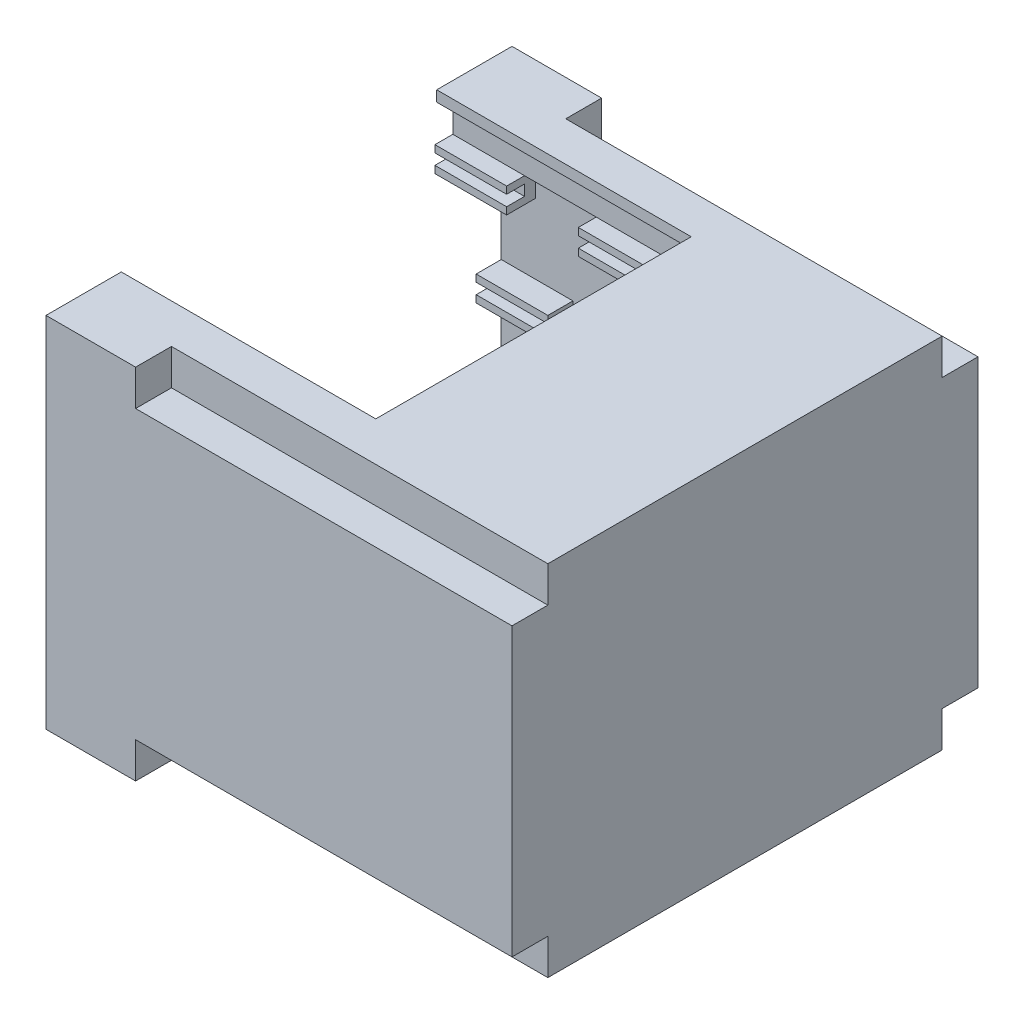
SolidWorks part; units mm, degrees
ref_plane "Front Plane" through (0, 0, 0) normal (0, 0, 1) x (1, 0, 0)
ref_plane "Top Plane" through (0, 0, 0) normal (0, 1, 0) x (1, 0, 0)
ref_plane "Right Plane" through (0, 0, 0) normal (1, 0, 0) x (0, 0, -1)
sketch "Sketch2" plane through (0, 0, 0) normal (0, 1, 0) x (1, 0, 0)
  line L1 (0, 0) -> (130, 0)
  line L2 (0, 0) -> (0, 130)
  line L3 (0, 130) -> (130, 130)
  line L4 (130, 0) -> (130, 130)
  dimension "D1" = 130
  dimension "D2" = 130
extrude "Boss-Extrude1" add sketch "Sketch2" along normal blind 100
sketch "Sketch3" plane through (0, 0, 0) normal (-1, 0, 0) x (0, 0, 1)
  line L0 (-130, 100) -> (0, 100) construction
  line L1 (-117, 13) -> (-13, 13)
  line L2 (-117, 13) -> (-117, 87)
  line L3 (-117, 87) -> (-13, 87)
  line L4 (-13, 13) -> (-13, 87)
  line L5 (0, 100) -> (0, 0) construction
  line L6 (-130, 0) -> (0, 0) construction
  line L7 (-130, 100) -> (-130, 0) construction
  dimension "D1" = 13
  dimension "D2" = 13
  dimension "D3" = 13
  dimension "D4" = 13
extrude "Cut-Extrude1" cut sketch "Sketch3" against normal blind 127
sketch "Sketch4" plane through (130, 0, 0) normal (1, 0, 0) x (0, 0, -1)
  line L1 (0, 100) -> (10, 100)
  line L2 (0, 100) -> (0, 90)
  line L3 (0, 90) -> (10, 90)
  line L4 (10, 100) -> (10, 90)
  line L5 (130, 100) -> (120, 100)
  line L6 (130, 100) -> (130, 90)
  line L7 (130, 90) -> (120, 90)
  line L8 (120, 100) -> (120, 90)
  line L9 (0, 0) -> (10, 0)
  line L10 (0, 0) -> (0, 10)
  line L11 (0, 10) -> (10, 10)
  line L12 (10, 0) -> (10, 10)
  line L13 (130, 0) -> (120, 0)
  line L14 (130, 0) -> (130, 10)
  line L15 (130, 10) -> (120, 10)
  line L16 (120, 0) -> (120, 10)
  dimension "D1" = 10
  dimension "D2" = 10
  dimension "D3" = 10
  dimension "D4" = 10
  dimension "D5" = 10
  dimension "D6" = 10
  dimension "D7" = 10
  dimension "D8" = 10
extrude "Cut-Extrude3" cut sketch "Sketch4" against normal blind 105
sketch "Sketch5" plane through (0, 0, 0) normal (-1, 0, 0) x (0, 0, 1)
  line L0 (-130, 100) -> (0, 100) construction
  line L1 (-117, 87) -> (-13, 87)
  line L2 (-117, 87) -> (-117, 97)
  line L3 (-117, 97) -> (-13, 97)
  line L4 (-13, 87) -> (-13, 97)
  line L5 (-117, 13) -> (-13, 13)
  line L6 (-117, 13) -> (-117, 3)
  line L7 (-117, 3) -> (-13, 3)
  line L8 (-13, 13) -> (-13, 3)
  line L9 (-130, 0) -> (0, 0) construction
  line L10 (0, 100) -> (0, 0) construction
  dimension "D1" = 3
  dimension "D2" = 3
  dimension "D3" = 13
  dimension "D4" = 13
extrude "Cut-Extrude4" cut sketch "Sketch5" against normal blind 127
sketch "Sketch6" plane through (0, 0, 0) normal (-1, 0, 0) x (0, 0, 1)
  line L0 (-117, 97) -> (-117, 3) construction
  line L1 (-117, 87) -> (-127, 87)
  line L2 (-117, 87) -> (-117, 13)
  line L3 (-117, 13) -> (-127, 13)
  line L4 (-127, 87) -> (-127, 13)
  line L5 (-13, 3) -> (-13, 97) construction
  line L6 (-13, 87) -> (-3, 87)
  line L7 (-13, 87) -> (-13, 13)
  line L8 (-13, 13) -> (-3, 13)
  line L9 (-3, 87) -> (-3, 13)
  line L10 (-130, 100) -> (-130, 0) construction
  line L11 (0, 100) -> (0, 0) construction
  line L12 (-130, 100) -> (0, 100) construction
  line L13 (-130, 0) -> (0, 0) construction
  dimension "D1" = 3
  dimension "D2" = 3
  dimension "D3" = 13
  dimension "D4" = 13
  dimension "D5" = 13
  dimension "D6" = 13
extrude "Cut-Extrude5" cut sketch "Sketch6" against normal blind 127
sketch "Sketch7" plane through (0, 0, 0) normal (-1, 0, 0) x (0, 0, 1)
  line L0 (0, 100) -> (0, 0) construction
  line L1 (-130, 0) -> (0, 0) construction
  line L2 (-130, 100) -> (-130, 0) construction
  line L3 (-130, 100) -> (0, 100) construction
  circle A0 centre (-124, 94) radius 1.75
  circle A1 centre (-6, 94) radius 1.75
  circle A2 centre (-124, 6) radius 1.75
  circle A3 centre (-6, 6) radius 1.75
  dimension "D3" = 3.5
  dimension "D6" = 3.5
  dimension "D9" = 3.5
  dimension "D12" = 3.5
  dimension "D1" = 6
  dimension "D2" = 6
  dimension "D4" = 6
  dimension "D5" = 6
  dimension "D7" = 6
  dimension "D8" = 6
  dimension "D10" = 6
  dimension "D11" = 6
extrude "Cut-Extrude6" cut sketch "Sketch7" against normal blind 20
sketch "Sketch8" plane through (0, 0, 0) normal (-1, 0, 0) x (0, 0, 1)
  line L1 (-117, 87) -> (-120, 87)
  line L2 (-117, 87) -> (-117, 90)
  line L3 (-117, 90) -> (-120, 90)
  line L4 (-120, 87) -> (-120, 90)
  line L5 (-13, 87) -> (-10, 87)
  line L6 (-13, 87) -> (-13, 90)
  line L7 (-13, 90) -> (-10, 90)
  line L8 (-10, 87) -> (-10, 90)
  line L9 (-117, 13) -> (-120, 13)
  line L10 (-117, 13) -> (-117, 10)
  line L11 (-117, 10) -> (-120, 10)
  line L12 (-120, 13) -> (-120, 10)
  line L13 (-13, 13) -> (-10, 13)
  line L14 (-13, 13) -> (-13, 10)
  line L15 (-13, 10) -> (-10, 10)
  line L16 (-10, 13) -> (-10, 10)
  dimension "D1" = 3
  dimension "D2" = 3
  dimension "D3" = 3
  dimension "D4" = 3
  dimension "D5" = 3
  dimension "D6" = 3
  dimension "D7" = 3
  dimension "D8" = 3
extrude "Cut-Extrude7" cut sketch "Sketch8" against normal blind 5
sketch "Sketch9" plane through (0, 3, 0) normal (0, 1, 0) x (1, 0, 0)
  line L1 (0, 117) -> (85, 117)
  line L2 (0, 117) -> (0, 57)
  line L3 (0, 57) -> (85, 57)
  line L4 (85, 117) -> (85, 57)
  dimension "D1" = 60
  dimension "D2" = 85
extrude "Boss-Extrude2" add sketch "Sketch9" along normal blind 15
sketch "Sketch11" plane through (0, 13, 0) normal (0, 1, 0) x (1, 0, 0)
  line L0 (0, 127) -> (0, 120) construction
  line L5 (85, 117) -> (0, 117)
  line L6 (85, 117) -> (85, 123)
  line L7 (85, 123) -> (0, 123)
  line L8 (0, 117) -> (0, 123)
  dimension "D1" = 6
extrude "Boss-Extrude5" add sketch "Sketch11" along normal blind 5
sketch "Sketch12" plane through (0, 18, 0) normal (0, 1, 0) x (1, 0, 0)
  line L0 (85, 57) -> (85, 123) construction
  line L1 (0, 123) -> (85, 123)
  line L2 (0, 123) -> (0, 120)
  line L3 (0, 120) -> (85, 120)
  line L4 (85, 123) -> (85, 120)
  dimension "D1" = 3
extrude "Cut-Extrude9" cut sketch "Sketch12" against normal blind 4
sketch "Sketch13" plane through (0, 18, 0) normal (0, 1, 0) x (1, 0, 0)
  line L0 (85, 57) -> (85, 120) construction
  line L1 (82, 117) -> (0, 117)
  line L2 (82, 117) -> (82, 60)
  line L3 (82, 60) -> (0, 60)
  line L4 (0, 117) -> (0, 60)
  line L5 (0, 57) -> (85, 57) construction
  line L6 (0, 120) -> (85, 120) construction
  line L7 (0, 120) -> (0, 57) construction
  dimension "D1" = 3
  dimension "D2" = 3
  dimension "D3" = 3
  dimension "D4" = 0
extrude "Cut-Extrude10" cut sketch "Sketch13" against normal blind 15
sketch "Sketch15" plane through (5, 0, 0) normal (-1, 0, 0) x (0, 0, 1)
  line L1 (-120, 13) -> (-117, 13)
  line L2 (-120, 13) -> (-120, 10)
  line L3 (-120, 10) -> (-117, 10)
  line L4 (-117, 13) -> (-117, 10)
extrude "Boss-Extrude7" add sketch "Sketch15" along normal blind 5
sketch "Sketch16" plane through (0, 0, -60) normal (0, 0, -1) x (-1, 0, 0)
  line L0 (0, 3) -> (0, 18) construction
  line L1 (-82, 18) -> (0, 18)
  line L2 (-82, 18) -> (-82, 16)
  line L3 (-82, 16) -> (0, 16)
  line L4 (0, 18) -> (0, 16)
  line L5 (-82, 3) -> (-82, 18) construction
  line L6 (-82, 13) -> (0, 13)
  line L7 (-82, 13) -> (-82, 11)
  line L8 (-82, 11) -> (0, 11)
  line L9 (0, 13) -> (0, 11)
  dimension "D1" = 2
  dimension "D2" = 2
  dimension "D3" = 3
extrude "Boss-Extrude8" add sketch "Sketch16" along normal blind 57
sketch "Sketch17" plane through (0, 18, 0) normal (0, 1, 0) x (1, 0, 0)
  line L0 (0, 120) -> (0, 57) construction
  line L1 (0, 112) -> (77, 112)
  line L2 (0, 112) -> (0, 65)
  line L3 (0, 65) -> (77, 65)
  line L4 (77, 112) -> (77, 65)
  line L5 (0, 57) -> (85, 57) construction
  line L6 (85, 57) -> (85, 120) construction
  line L7 (0, 120) -> (85, 120) construction
  dimension "D1" = 8
  dimension "D2" = 8
  dimension "D3" = 8
extrude "Cut-Extrude11" cut sketch "Sketch17" against normal blind 10
sketch "Sketch19" plane through (0, 0, -117) normal (0, 0, 1) x (1, 0, 0)
  line L1 (0, 11) -> (7, 11)
  line L2 (0, 11) -> (0, 9)
  line L3 (0, 9) -> (7, 9)
  line L4 (7, 11) -> (7, 9)
  line L5 (0, 13) -> (7, 13)
  line L6 (0, 13) -> (0, 14)
  line L7 (0, 14) -> (7, 14)
  line L8 (7, 13) -> (7, 14)
  dimension "D1" = 2
  dimension "D2" = 7
  dimension "D3" = 7
  dimension "D4" = 1
extrude "Boss-Extrude9" add sketch "Sketch19" along normal blind 1
sketch "Sketch21" plane through (0, 0, 0) normal (-1, 0, 0) x (0, 0, 1)
  line L0 (-130, 0) -> (0, 0) construction
  line L1 (-120, 13) -> (-117, 13)
  line L2 (-120, 13) -> (-120, 10)
  line L3 (-120, 10) -> (-117, 10)
  line L4 (-117, 13) -> (-117, 10)
  line L5 (-130, 100) -> (-130, 0) construction
  dimension "D1" = 3
  dimension "D2" = 3
  dimension "D3" = 10
  dimension "D4" = 10
extrude "Cut-Extrude15" cut sketch "Sketch21" against normal blind 5
sketch "Sketch22" plane through (127, 0, 0) normal (-1, 0, 0) x (0, 0, 1)
  line L0 (-127, 87) -> (-127, 13) construction
  line L1 (-127, 50) -> (-3, 50)
  line L2 (-127, 50) -> (-127, 43)
  line L3 (-127, 43) -> (-3, 43)
  line L4 (-3, 50) -> (-3, 43)
  line L5 (-3, 13) -> (-3, 87) construction
  line L6 (-65, 18) -> (-112, 18) construction
  dimension "D1" = 7
  dimension "D2" = 25
extrude "Boss-Extrude10" add sketch "Sketch22" along normal blind 127
sketch "Sketch23" plane through (0, 0, 0) normal (-1, 0, 0) x (0, 0, 1)
  line L0 (-3, 50) -> (-127, 50) construction
  line L1 (-125, 48) -> (-5, 48)
  line L2 (-125, 48) -> (-125, 45)
  line L3 (-125, 45) -> (-5, 45)
  line L4 (-5, 48) -> (-5, 45)
  line L5 (-130, 100) -> (-130, 0) construction
  dimension "D1" = 120
  dimension "D2" = 3
  dimension "D3" = 2
  dimension "D4" = 5
extrude "Cut-Extrude16" cut sketch "Sketch23" against normal blind 125
sketch "Sketch24" plane through (0, 50, 0) normal (0, 1, 0) x (1, 0, 0)
  line L0 (0, 3) -> (0, 127) construction
  line L1 (0, 120) -> (120, 120)
  line L2 (0, 120) -> (0, 10)
  line L3 (0, 10) -> (120, 10)
  line L4 (120, 120) -> (120, 10)
  line L5 (127, 3) -> (127, 127) construction
  line L6 (0, 127) -> (127, 127) construction
  line L7 (0, 3) -> (127, 3) construction
  dimension "D1" = 7
  dimension "D2" = 7
  dimension "D3" = 7
extrude "Cut-Extrude17" cut sketch "Sketch24" against normal blind 15
sketch "Sketch25" plane through (0, 100, 0) normal (0, 1, 0) x (1, 0, 0)
  line L0 (0, 130) -> (0, 0) construction
  line L1 (0, 109) -> (71, 109)
  line L2 (0, 109) -> (0, 21)
  line L3 (0, 21) -> (71, 21)
  line L4 (71, 109) -> (71, 21)
  line L6 (25, 120) -> (130, 120) construction
  dimension "D1" = 71
  dimension "D2" = 88
  dimension "D3" = 11
extrude "Cut-Extrude18" cut sketch "Sketch25" against normal blind 15
sketch "Sketch27" plane through (127, 0, 0) normal (-1, 0, 0) x (0, 0, 1)
  line L0 (-13, 97) -> (-117, 97) construction
  line L1 (-116.5, 97) -> (-13.5, 97)
  line L2 (-116.5, 97) -> (-116.5, 80)
  line L3 (-116.5, 80) -> (-13.5, 80)
  line L4 (-13.5, 97) -> (-13.5, 80)
  line L5 (-117, 97) -> (-117, 87) construction
  dimension "D1" = 103
  dimension "D2" = 0.5
  dimension "D3" = 17
extrude "Boss-Extrude11" add sketch "Sketch27" along normal blind 127
sketch "Sketch28" plane through (0, 0, 0) normal (-1, 0, 0) x (0, 0, 1)
  line L0 (-21, 97) -> (-109, 97) construction
  line L1 (-113.5, 85) -> (-16.5, 85)
  line L2 (-113.5, 85) -> (-113.5, 82)
  line L3 (-113.5, 82) -> (-16.5, 82)
  line L4 (-16.5, 85) -> (-16.5, 82)
  line L5 (-113.5, 97) -> (-16.5, 97)
  line L6 (-113.5, 97) -> (-113.5, 87)
  line L7 (-113.5, 87) -> (-16.5, 87)
  line L8 (-16.5, 97) -> (-16.5, 87)
  line L9 (-116.5, 80) -> (-13.5, 80) construction
  line L10 (-116.5, 97) -> (-116.5, 80) construction
  line L11 (-13.5, 80) -> (-13.5, 97) construction
  line L12 (-116.5, 97) -> (-116.5, 80) construction
  dimension "D1" = 10
  dimension "D2" = 0
  dimension "D3" = 2
  dimension "D4" = 3
  dimension "D5" = 3
  dimension "D6" = 3
  dimension "D7" = 3
  dimension "D8" = 3
extrude "Cut-Extrude19" cut sketch "Sketch28" against normal blind 120
sketch "Sketch29" plane through (0, 80, 0) normal (0, -1, 0) x (1, 0, 0)
  line L0 (0, -116.5) -> (127, -116.5) construction
  line L1 (127, -13.5) -> (123, -13.5)
  line L2 (127, -13.5) -> (127, -116.5)
  line L3 (127, -116.5) -> (123, -116.5)
  line L4 (123, -13.5) -> (123, -116.5)
  line L5 (0, -116.5) -> (0, -13.5) construction
  dimension "D1" = 123
extrude "Cut-Extrude20" cut sketch "Sketch29" against normal blind 17
sketch "Sketch30" plane through (0, 87, 0) normal (0, 1, 0) x (1, 0, 0)
  line L0 (0, 113.5) -> (0, 16.5) construction
  line L1 (0, 108.5) -> (115, 108.5)
  line L2 (0, 108.5) -> (0, 21.5)
  line L3 (0, 21.5) -> (115, 21.5)
  line L4 (115, 108.5) -> (115, 21.5)
  line L5 (120, 113.5) -> (0, 113.5) construction
  line L6 (120, 16.5) -> (0, 16.5) construction
  line L7 (120, 113.5) -> (120, 16.5) construction
  dimension "D1" = 5
  dimension "D2" = 5
  dimension "D3" = 5
extrude "Cut-Extrude21" cut sketch "Sketch30" against normal blind 17
sketch "Sketch31" plane through (0, 50, 0) normal (0, 1, 0) x (1, 0, 0)
  line L0 (0, 127) -> (127, 127) construction
  line L1 (20, 127) -> (40, 127)
  line L2 (20, 127) -> (20, 3)
  line L3 (20, 3) -> (40, 3)
  line L4 (40, 127) -> (40, 3)
  line L5 (0, 3) -> (127, 3) construction
  line L6 (0, 120) -> (0, 127) construction
  dimension "D1" = 20
  dimension "D2" = 20
extrude "Cut-Extrude22" cut sketch "Sketch31" against normal blind 36 and the other way blind 37
sketch "Sketch32" plane through (0, 0, -127) normal (0, 0, 1) x (1, 0, 0)
  line L0 (127, 43) -> (127, 13) construction
  line L1 (82, 3) -> (0, 3) construction
  circle A0 centre (94, 25) radius 3
  circle A1 centre (110, 25) radius 3
  dimension "D1" = 6
  dimension "D2" = 6
  dimension "D3" = 17
  dimension "D4" = 33
  dimension "D5" = 22
  dimension "D6" = 22
extrude "Cut-Extrude23" cut sketch "Sketch32" against normal blind 36
sketch "Sketch34" plane through (0, 0, -130) normal (0, 0, -1) x (-1, 0, 0)
  text T0 "OUT"
  text T1 "IN"
extrude "Cut-Extrude24" cut sketch "Sketch34" against normal blind 0.5
